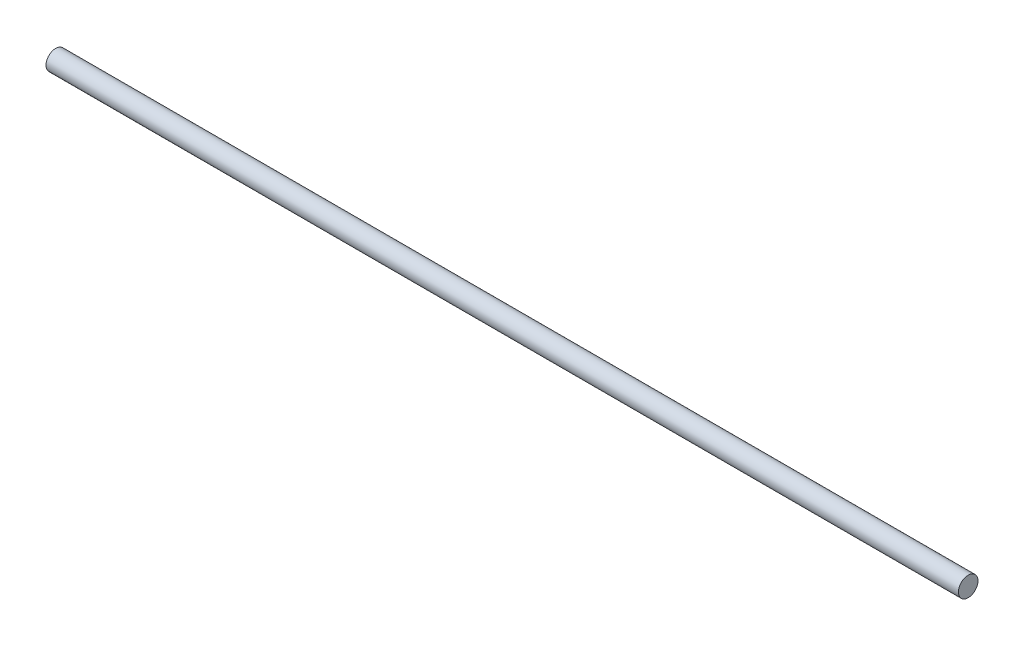
SolidWorks part; units mm, degrees
ref_plane "Front Plane" through (0, 0, 0) normal (0, 0, 1) x (1, 0, 0)
ref_plane "Top Plane" through (0, 0, 0) normal (0, 1, 0) x (1, 0, 0)
ref_plane "Right Plane" through (0, 0, 0) normal (1, 0, 0) x (0, 0, -1)
sketch "Sketch1" plane through (0, 0, 0) normal (1, 0, 0) x (0, 0, -1)
  circle A0 centre (0, 0) radius 3.81
  dimension "D1" = 7.62
extrude "Boss-Extrude1" add sketch "Sketch1" along normal blind 355.6
